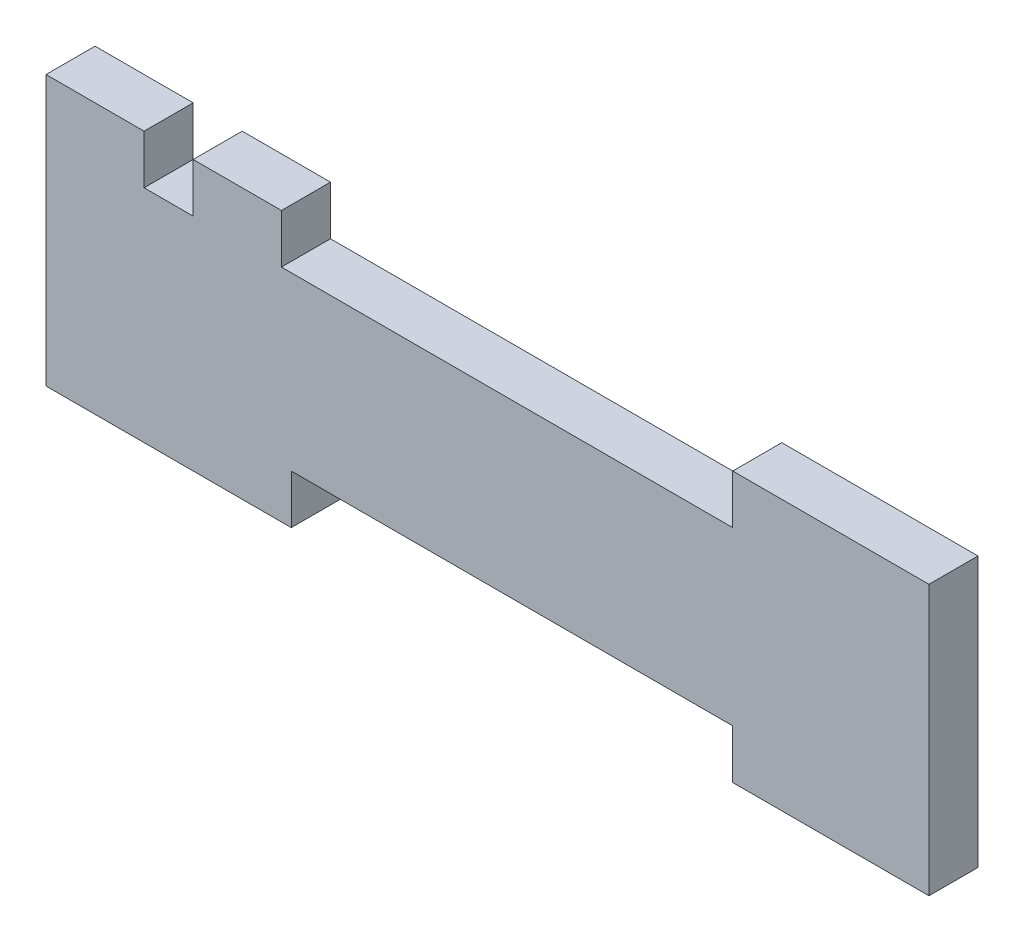
SolidWorks part; units mm, degrees
ref_plane "Front Plane" through (0, 0, 0) normal (0, 0, 1) x (1, 0, 0)
ref_plane "Top Plane" through (0, 0, 0) normal (0, 1, 0) x (1, 0, 0)
ref_plane "Right Plane" through (0, 0, 0) normal (1, 0, 0) x (0, 0, -1)
sketch "Sketch1" plane through (0, 0, 0) normal (0, 0, 1) x (1, 0, 0)
  line L1 (0, 0) -> (-90, 0)
  line L2 (0, 0) -> (0, 17.5)
  line L3 (0, 17.5) -> (-90, 17.5)
  line L4 (-90, 0) -> (-90, 17.5)
  line L5 (-90, 17.5) -> (-65, 17.5)
  line L6 (-90, 17.5) -> (-90, 22.5)
  line L7 (-90, 22.5) -> (-65, 22.5)
  line L8 (-65, 17.5) -> (-65, 22.5)
  line L9 (-80, 22.5) -> (-75, 22.5)
  line L10 (-80, 22.5) -> (-80, 17.5)
  line L11 (-80, 17.5) -> (-75, 17.5)
  line L12 (-75, 22.5) -> (-75, 17.5)
  line L13 (0, 17.5) -> (-20, 17.5)
  line L14 (0, 17.5) -> (0, 22.5)
  line L15 (0, 22.5) -> (-20, 22.5)
  line L16 (-20, 17.5) -> (-20, 22.5)
  line L17 (0, 0) -> (-20, 0)
  line L18 (0, 0) -> (0, -5)
  line L19 (0, -5) -> (-20, -5)
  line L20 (-20, 0) -> (-20, -5)
  line L21 (-90, 0) -> (-65, 0)
  line L22 (-90, 0) -> (-90, -5)
  line L23 (-90, -5) -> (-65, -5)
  line L24 (-65, 0) -> (-65, -5)
  dimension "D1" = 90
  dimension "D2" = 17.5
  dimension "D3" = 25
  dimension "D4" = 5
  dimension "D5" = 5
  dimension "D6" = 10
  dimension "D7" = 20
  dimension "D8" = 20
  dimension "D9" = 5
  dimension "D10" = 25
  dimension "D11" = 5
  dimension "D12" = 5
extrude "Boss-Extrude1" add sketch "Sketch1" along normal blind 5 contours L4 L1 L2 L3 L5 | L10 L7 L6 L5 | L7 L12 L3 L8 | L24 L1 L22 L23 | L1 L20 L19 L18 | L16 L3 L14 L15
sketch "Sketch2" plane through (-65, 0, 0) normal (1, 0, 0) x (0, 0, -1)
  line L4 (0, 17.5) -> (0, 22.5)
  line L5 (0, 22.5) -> (-5, 22.5)
  line L6 (-5, 22.5) -> (-5, 17.5)
  line L7 (-5, 17.5) -> (0, 17.5)
  line L8 (0, 17.5) -> (0, 22.5)
  line L9 (0, 22.5) -> (-5, 22.5)
  line L10 (-5, 22.5) -> (-5, 17.5)
  line L11 (-5, 17.5) -> (0, 17.5)
  dimension "D1" = 0
extrude "Cut-Extrude1" cut sketch "Sketch2" against normal blind 1
